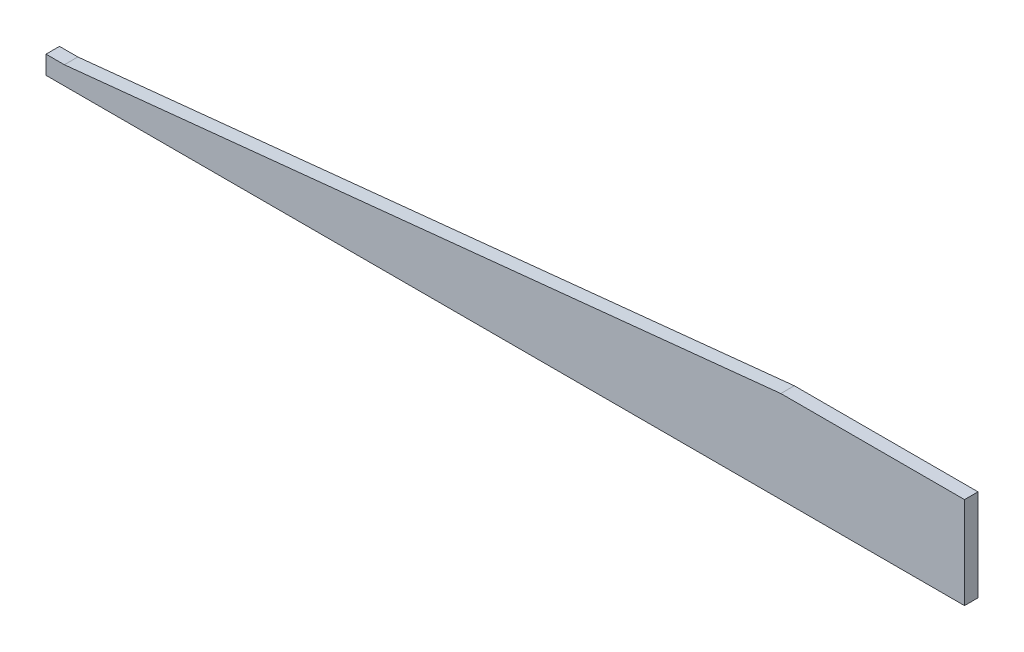
SolidWorks part; units mm, degrees
ref_plane "Front Plane" through (0, 0, 0) normal (0, 0, 1) x (1, 0, 0)
ref_plane "Top Plane" through (0, 0, 0) normal (0, 1, 0) x (1, 0, 0)
ref_plane "Right Plane" through (0, 0, 0) normal (1, 0, 0) x (0, 0, -1)
sketch "Esquisse1" plane through (0, 0, 0) normal (0, 0, 1) x (1, 0, 0)
  line L0 (30, 30) -> (1200, 150)
  line L1 (1200, 150) -> (1500, 150)
  line L2 (30, 30) -> (0, 30)
  line L3 (0, 30) -> (0, 0)
  line L4 (0, 0) -> (1500, 0)
  line L5 (1500, 0) -> (1500, 150)
  point P2 (1500, 0)
  dimension "D1" = 1500
  dimension "D2" = 30
  dimension "D3" = 30
  dimension "D4" = 300
  dimension "D5" = 150
extrude "Boss.-Extru.1" add sketch "Esquisse1" along normal blind 22
